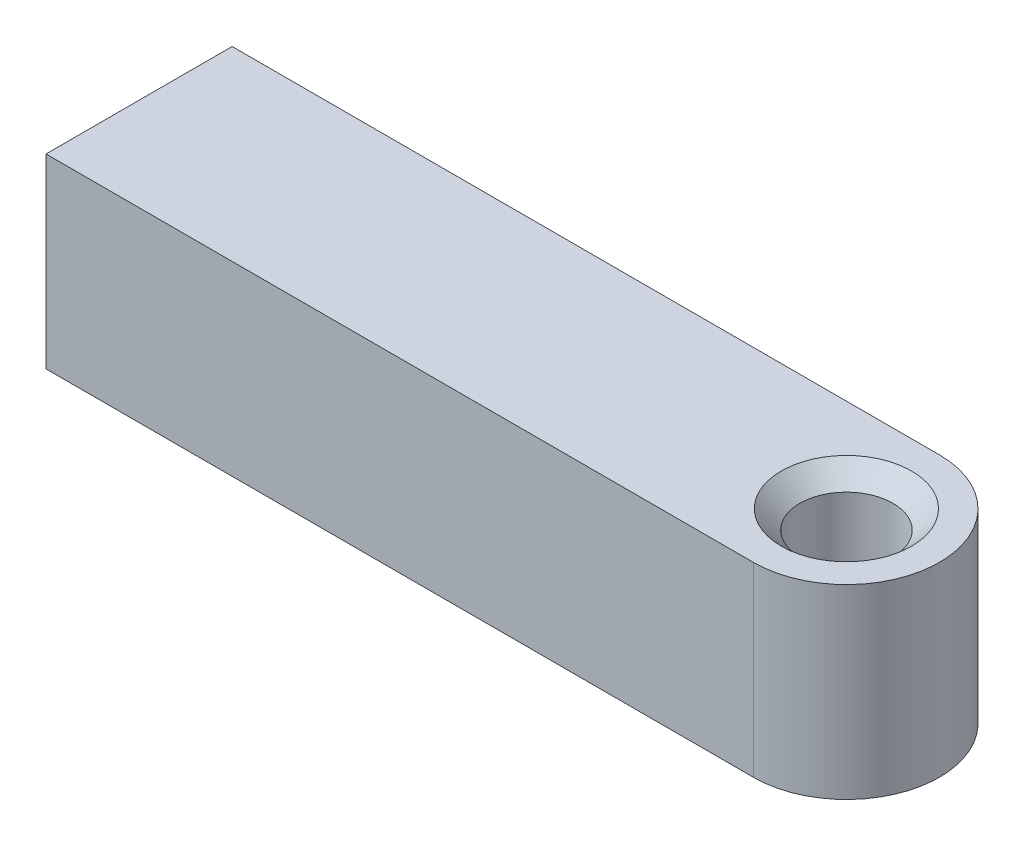
SolidWorks part; units mm, degrees
ref_plane "Plan de face" through (0, 0, 0) normal (0, 0, 1) x (1, 0, 0)
ref_plane "Plan de dessus" through (0, 0, 0) normal (0, 1, 0) x (1, 0, 0)
ref_plane "Plan de droite" through (0, 0, 0) normal (1, 0, 0) x (0, 0, -1)
sketch "Esquisse1" plane through (0, 0, 0) normal (0, 1, 0) x (1, 0, 0)
  line L0 (0, 5) -> (-38, 5)
  line L1 (0, -5) -> (-38, -5)
  line L2 (-38, -5) -> (-38, 5)
  arc A1 (0, -5) -> (0, 5) centre (0, 0) ccw
extrude "Boss.-Extru.1" add sketch "Esquisse1" along normal blind 10
sketch "Esquisse2" plane through (0, 10, 0) normal (0, 1, 0) x (-1, 0, 0)
  line L0 (-5, 0) -> (5.8637, 0) construction
  line L1 (0, -5) -> (0, 5) construction
  arc A0 (0, 5) -> (0, -5) centre (0, 0) ccw construction
hole_wizard "Trou taraudé M61" positions "Esquisse4" profile "Esquisse3" tap size "M6" standard "ISO" end condition through all
sketch "Esquisse4" plane through (0, 10, 0) normal (0, 1, 0) x (-1, 0, 0)
  point P0 (0, 0)
sketch "Esquisse3" plane through (0, 10, 0) normal (1, 0, 0) x (0, 0, 1)
  line L0 (0, 0) -> (0, 10)
  line L1 (0, 10) -> (3.5, 10)
  line L2 (2.5, 9) -> (2.5, 1)
  line L3 (2.5, 1) -> (3.5, 0)
  line L5 (3.5, 0) -> (0, 0)
  line L6 (-2.5, 1) -> (-3.5, 0) construction
  line L7 (3.5, 10) -> (2.5, 9)
  line L8 (-3.5, 10) -> (-2.5, 9) construction
  line L11 (0, -6.35) -> (0, 107.95) construction
  dimension "Diamètre du trou pour taraudage jusqu'au prochain" = 5
  dimension "Profondeur du trou pour taraudage jusqu'au prochain" = 10
  dimension "Diamètre du fraisage entrant" = 7
  dimension "Angle du fraisage entrant" = 90
  dimension "Diamètre du fraisage débouchant" = 7
  dimension "Angle du fraisage débouchant" = 90
cosmetic thread "Filetage de perçage1" parameters "D2"=6
